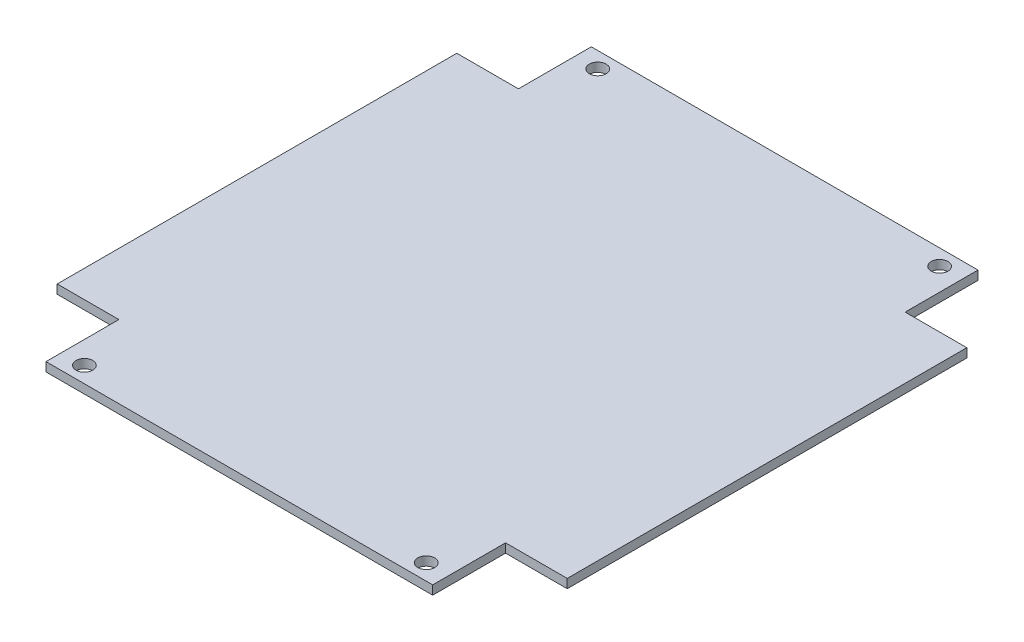
SolidWorks part; units mm, degrees
ref_plane "Front Plane" through (0, 0, 0) normal (0, 0, 1) x (1, 0, 0)
ref_plane "Top Plane" through (0, 0, 0) normal (0, 1, 0) x (1, 0, 0)
ref_plane "Right Plane" through (0, 0, 0) normal (1, 0, 0) x (0, 0, -1)
sketch "Sketch1" plane through (0, 0, 0) normal (0, 1, 0) x (1, 0, 0)
  line L1 (-45.5, 48.65) -> (45.5, 48.65)
  line L2 (-45.5, 48.65) -> (-45.5, -48.65)
  line L3 (-45.5, -48.65) -> (45.5, -48.65)
  line L4 (45.5, 48.65) -> (45.5, -48.65)
  dimension "D1" = 97.3
  dimension "D2" = 91
  dimension "D3" = 45.5
  dimension "D4" = 48.65
extrude "Boss-Extrude1" add sketch "Sketch1" along normal blind 1.6
sketch "Sketch2" plane through (0, 1.6, 0) normal (0, 1, 0) x (1, 0, 0)
  line L1 (-45.5, 48.65) -> (-34.5, 48.65)
  line L2 (-45.5, 48.65) -> (-45.5, 35.65)
  line L3 (-45.5, 35.65) -> (-34.5, 35.65)
  line L4 (-34.5, 48.65) -> (-34.5, 35.65)
  line L5 (45.5, 48.65) -> (34.5, 48.65)
  line L6 (45.5, 48.65) -> (45.5, 35.65)
  line L7 (45.5, 35.65) -> (34.5, 35.65)
  line L8 (34.5, 48.65) -> (34.5, 35.65)
  line L9 (-45.5, -48.65) -> (-34.5, -48.65)
  line L10 (-45.5, -48.65) -> (-45.5, -35.65)
  line L11 (-45.5, -35.65) -> (-34.5, -35.65)
  line L12 (-34.5, -48.65) -> (-34.5, -35.65)
  line L13 (45.5, -48.65) -> (34.5, -48.65)
  line L14 (45.5, -48.65) -> (45.5, -35.65)
  line L15 (45.5, -35.65) -> (34.5, -35.65)
  line L16 (34.5, -48.65) -> (34.5, -35.65)
  dimension "D1" = 11
  dimension "D2" = 13
  dimension "D3" = 13
  dimension "D4" = 11
  dimension "D5" = 11
  dimension "D6" = 13
  dimension "D7" = 11
  dimension "D8" = 13
extrude "Cut-Extrude1" cut sketch "Sketch2" against normal blind 1.6
sketch "Sketch3" plane through (0, 1.6, 0) normal (0, 1, 0) x (1, 0, 0)
  line L0 (-34.5, 35.65) -> (-34.5, 48.65) construction
  line L1 (34.5, 48.65) -> (34.5, 35.65) construction
  line L2 (0, 48.65) -> (0, -48.65) construction
  line L3 (34.5, 48.65) -> (-34.5, 48.65) construction
  line L4 (-34.5, -48.65) -> (34.5, -48.65) construction
  line L5 (-45.5, 0) -> (45.5, 0) construction
  line L6 (-45.5, 35.65) -> (-45.5, -35.65) construction
  line L7 (45.5, -35.65) -> (45.5, 35.65) construction
  circle A0 centre (-30.5, 45.8) radius 1.5
  circle A1 centre (30.5, 45.8) radius 1.5
  dimension "D2" = 3
  dimension "D3" = 3
  dimension "D1" = 69
  dimension "D4" = 61
  dimension "D5" = 30.5
  dimension "D6" = 45.8
extrude "Cut-Extrude2" cut sketch "Sketch3" against normal blind 1.6
mirror "Mirror1" about plane through (0, 0, 0) normal (0, 0, 1) of "Cut-Extrude2"
